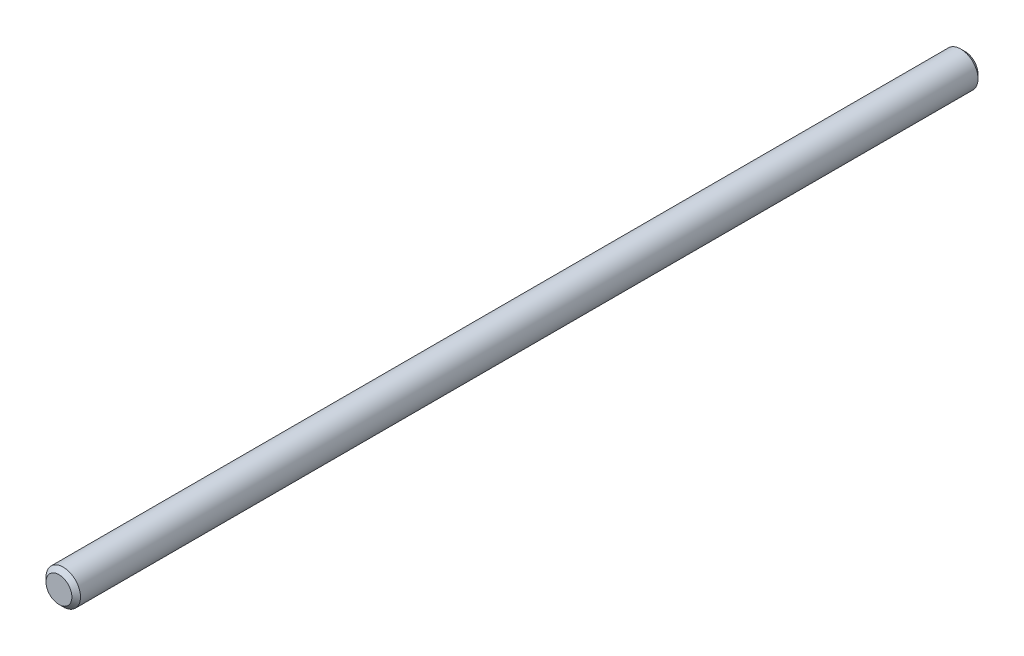
SolidWorks part; units mm, degrees
ref_plane "Front Plane" through (0, 0, 0) normal (0, 0, 1) x (1, 0, 0)
ref_plane "Top Plane" through (0, 0, 0) normal (0, 1, 0) x (1, 0, 0)
ref_plane "Right Plane" through (0, 0, 0) normal (1, 0, 0) x (0, 0, -1)
sketch "Sketch1" plane through (0, 0, 0) normal (0, 0, 1) x (1, 0, 0)
  circle A0 centre (0, 0) radius 2
  dimension "D1" = 4
extrude "Boss-Extrude1" add sketch "Sketch1" along normal mid plane 105
cosmetic thread "Cosmetic Thread1" parameters "D1"=16, "D2"=3.22
cosmetic thread "Cosmetic Thread2" parameters "D1"=8, "D2"=3.22
chamfer "Chamfer1" distance 0.5 angle 45 2 edges at (2, 0, -52.5) (2, 0, 52.5)
